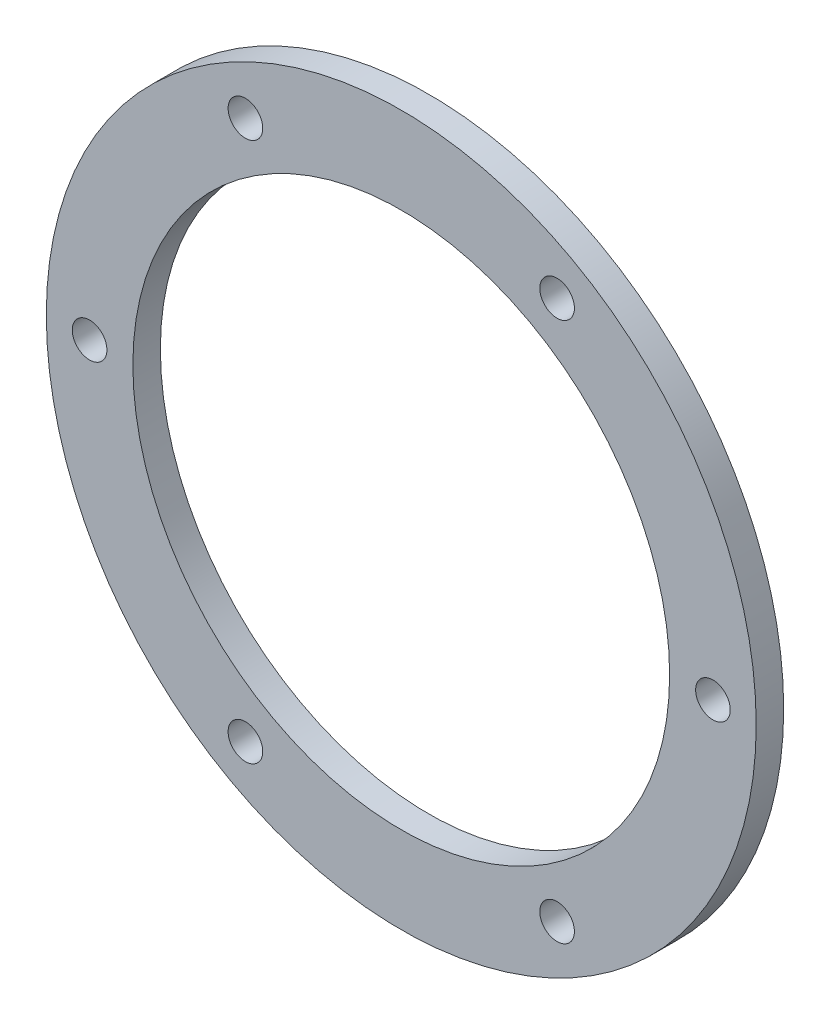
SolidWorks part; units mm, degrees
ref_plane "Front Plane" through (0, 0, 0) normal (0, 0, 1) x (1, 0, 0)
ref_plane "Top Plane" through (0, 0, 0) normal (0, 1, 0) x (1, 0, 0)
ref_plane "Right Plane" through (0, 0, 0) normal (1, 0, 0) x (0, 0, -1)
sketch "Sketch1" plane through (0, 0, 0) normal (0, 0, 1) x (1, 0, 0)
  circle A0 centre (0, 0) radius 31
  circle A1 centre (0, 0) radius 41
  dimension "D1" = 82
  dimension "D2" = 62
extrude "Boss-Extrude1" add sketch "Sketch1" along normal blind 3.175
sketch "Sketch2" plane through (0, 0, 3.175) normal (0, 0, 1) x (1, 0, 0)
  line L0 (0, 0) -> (0, 41) construction
  line L1 (0, 0) -> (-20.5, 35.507) construction
  circle A0 centre (0, 0) radius 41 construction
  circle A1 centre (-18, 31.1769) radius 2
  circle A2 centre (18, 31.1769) radius 2
  circle A3 centre (36, 0) radius 2
  circle A4 centre (18, -31.1769) radius 2
  circle A5 centre (-18, -31.1769) radius 2
  circle A6 centre (-36, 0) radius 2
  point P22 (0, 0)
  dimension "D2" = 4
  dimension "D1" = 30
  dimension "D4" = 36
  dimension "D3" = 6
extrude "Cut-Extrude2" cut sketch "Sketch2" against normal through all
